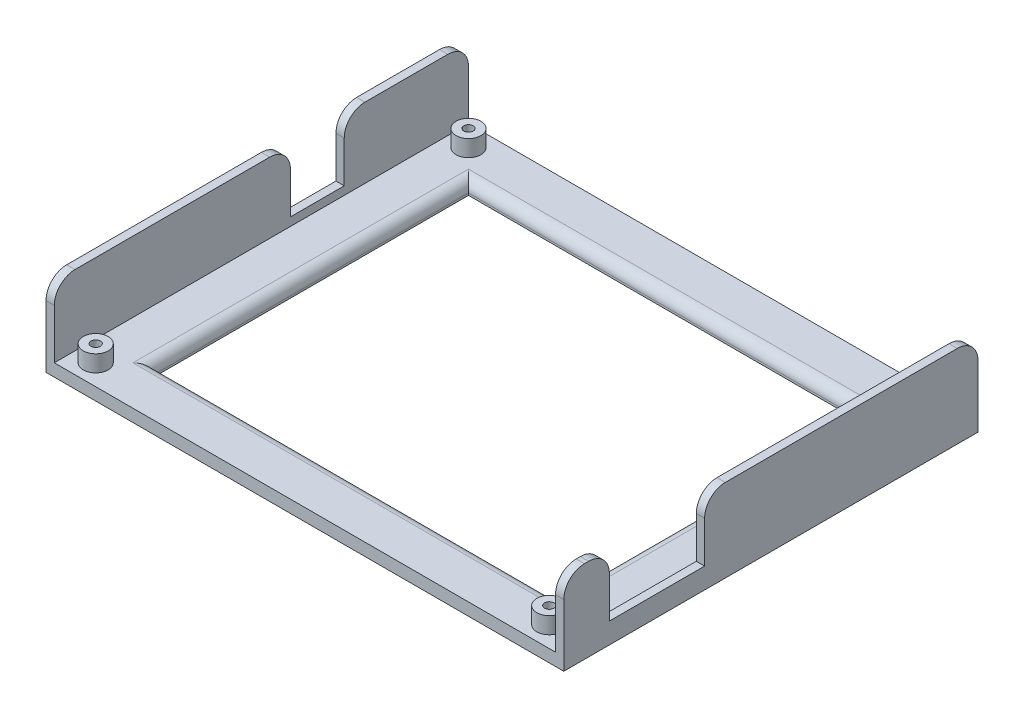
SolidWorks part; units mm, degrees
ref_plane "Front Plane" through (0, 0, 0) normal (0, 0, 1) x (1, 0, 0)
ref_plane "Top Plane" through (0, 0, 0) normal (0, 1, 0) x (1, 0, 0)
ref_plane "Right Plane" through (0, 0, 0) normal (1, 0, 0) x (0, 0, -1)
sketch "Sketch1" plane through (0, 0, 0) normal (0, 1, 0) x (1, 0, 0)
  line L1 (-48.1783, 30.2846) -> (76.8217, 30.2846)
  line L2 (-48.1783, 30.2846) -> (-48.1783, -69.7154)
  line L3 (-48.1783, -69.7154) -> (76.8217, -69.7154)
  line L4 (76.8217, 30.2846) -> (76.8217, -69.7154)
  dimension "D1" = 100
  dimension "D2" = 125
extrude "Boss-Extrude1" add sketch "Sketch1" along normal blind 3
sketch "Sketch2" plane through (0, 3, 0) normal (0, 1, 0) x (1, 0, 0)
  line L0 (-48.1783, -69.7154) -> (76.8217, -69.7154) construction
  line L1 (76.8217, 30.2846) -> (74.8217, 30.2846)
  line L2 (76.8217, 30.2846) -> (76.8217, -69.7154)
  line L3 (76.8217, -69.7154) -> (74.8217, -69.7154)
  line L4 (74.8217, 30.2846) -> (74.8217, -69.7154)
  line L5 (76.8217, 30.2846) -> (-48.1783, 30.2846) construction
  line L6 (-48.1783, -69.7154) -> (-46.1783, -69.7154)
  line L7 (-48.1783, -69.7154) -> (-48.1783, 30.2846)
  line L8 (-48.1783, 30.2846) -> (-46.1783, 30.2846)
  line L9 (-46.1783, -69.7154) -> (-46.1783, 30.2846)
  dimension "D1" = 2
  dimension "D2" = 2
extrude "Boss-Extrude2" add sketch "Sketch2" along normal blind 17
sketch "Sketch3" plane through (0, 3, 0) normal (0, 1, 0) x (1, 0, 0)
  line L0 (-46.1783, -69.7154) -> (74.8217, -69.7154) construction
  line L1 (-46.1783, -69.7154) -> (-46.1783, 30.2846) construction
  line L3 (74.8217, 30.2846) -> (-46.1783, 30.2846) construction
  circle A0 centre (-41.1783, -64.7154) radius 3
  circle A1 centre (-41.1783, 25.2846) radius 3
  circle A2 centre (68.3156, 25.2846) radius 3
  circle A3 centre (68.3156, -64.7154) radius 3
  dimension "D1" = 6
  dimension "D2" = 5
  dimension "D3" = 5
  dimension "D4" = 5
extrude "Boss-Extrude4" add sketch "Sketch3" along normal blind 4
sketch "Sketch4" plane through (-48.1783, 0, 0) normal (-1, 0, 0) x (0, 0, 1)
  line L0 (-30.2846, 20) -> (69.7154, 20) construction
  line L1 (-0.2846, 20) -> (12.7154, 20)
  line L2 (-0.2846, 20) -> (-0.2846, 5)
  line L3 (-0.2846, 5) -> (12.7154, 5)
  line L4 (12.7154, 20) -> (12.7154, 5)
  line L5 (-30.2846, 20) -> (-30.2846, 0) construction
  line L6 (-30.2846, 0) -> (69.7154, 0) construction
  dimension "D1" = 13
  dimension "D2" = 30
  dimension "D3" = 5
extrude "Cut-Extrude1" cut sketch "Sketch4" against normal blind 2
sketch "Sketch5" plane through (76.8217, 0, 0) normal (1, 0, 0) x (0, 0, -1)
  line L0 (-69.7154, 20) -> (30.2846, 20) construction
  line L1 (-58.7154, 20) -> (-35.7154, 20)
  line L2 (-58.7154, 20) -> (-58.7154, 5)
  line L3 (-58.7154, 5) -> (-35.7154, 5)
  line L4 (-35.7154, 20) -> (-35.7154, 5)
  line L5 (-69.7154, 20) -> (-69.7154, 0) construction
  line L6 (-69.7154, 0) -> (30.2846, 0) construction
  dimension "D1" = 23
  dimension "D2" = 11
  dimension "D3" = 5
extrude "Cut-Extrude2" cut sketch "Sketch5" against normal blind 2
sketch "Sketch6" plane through (0, 7, 0) normal (0, 1, 0) x (1, 0, 0)
  circle A0 centre (-41.1783, -64.7154) radius 1.125
  circle A1 centre (-41.1783, 25.2846) radius 1.125
  circle A2 centre (68.3156, -64.7154) radius 1.125
  circle A3 centre (68.3156, 25.2846) radius 1.125
  dimension "D1" = 2.25
extrude "Cut-Extrude3" cut sketch "Sketch6" against normal blind 22
fillet "Fillet1" radius 5 4 edges at (75.8217, 20, 69.7154) (-47.1783, 20, 69.7154) (-47.1783, 20, -30.2846) (75.8217, 20, -30.2846)
fillet "Fillet2" radius 5 4 edges at (-47.1783, 20, -0.2846) (-47.1783, 20, 12.7154) (75.8217, 20, 58.7154) (75.8217, 20, 35.7154)
sketch "Sketch7" plane through (0, 3, 0) normal (0, 1, 0) x (1, 0, 0)
  line L0 (-46.1783, -69.7154) -> (74.8217, -69.7154) construction
  line L1 (62.9921, 18.2846) -> (-34.1783, 18.2846)
  line L2 (62.9921, 18.2846) -> (62.9921, -57.7154)
  line L3 (62.9921, -57.7154) -> (-34.1783, -57.7154)
  line L4 (-34.1783, 18.2846) -> (-34.1783, -57.7154)
  line L5 (74.8217, 30.2846) -> (-46.1783, 30.2846) construction
  dimension "D1" = 12
  dimension "D2" = 12
  dimension "D3" = 97.1703
  dimension "D4" = 12
extrude "Cut-Extrude4" cut sketch "Sketch7" against normal blind 22
fillet "Fillet3" radius 2.5 4 edges at (-34.1783, 3, 19.7154) (14.4069, 3, -18.2846) (62.9921, 3, 19.7154) (14.4069, 3, 57.7154)
